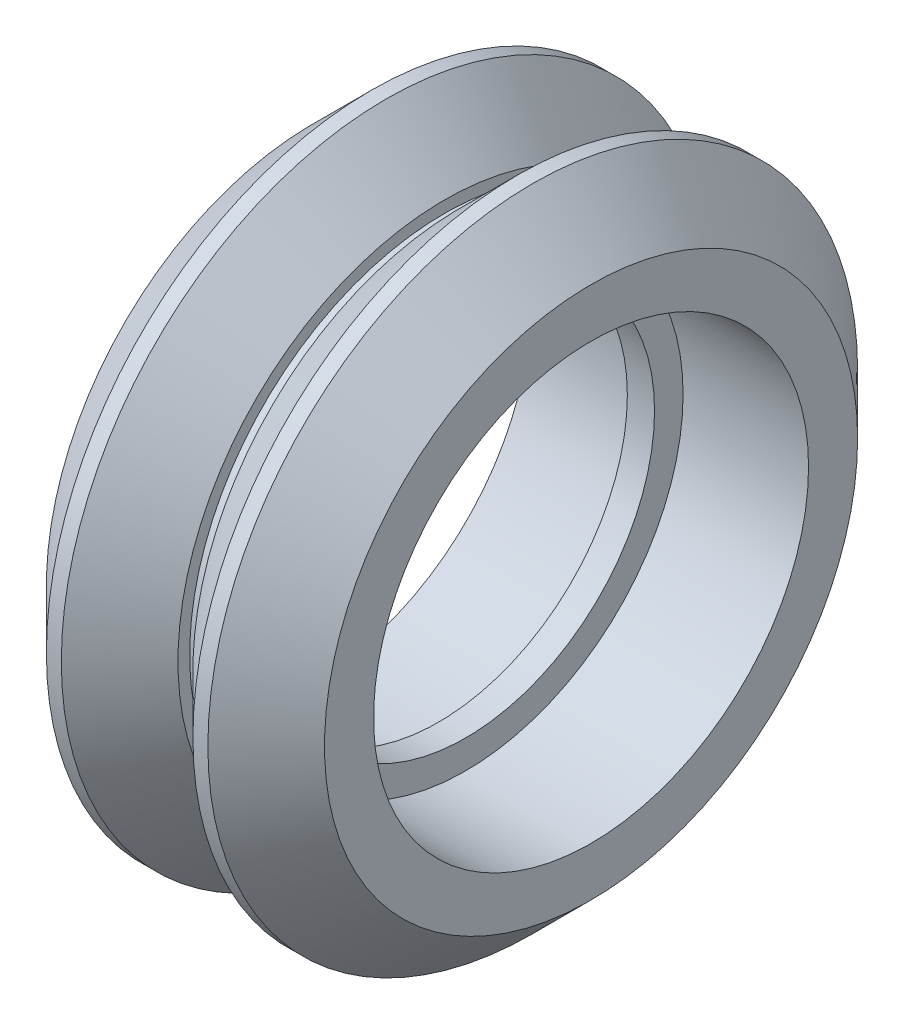
SolidWorks part; units mm, degrees
material "Chrome Stainless Steel"
ref_plane "Front Plane" through (0, 0, 0) normal (0, 0, 1) x (1, 0, 0)
ref_plane "Top Plane" through (0, 0, 0) normal (0, 1, 0) x (1, 0, 0)
ref_plane "Right Plane" through (0, 0, 0) normal (1, 0, 0) x (0, 0, -1)
sketch "Sketch1" plane through (0, 0, 0) normal (0, 0, 1) x (1, 0, 0)
  line L0 (0.5, 6.95) -> (-0.5, 6.95)
  line L1 (-0.5, 6.95) -> (-0.5, 8)
  line L2 (-0.5, 8) -> (-5.115, 8)
  line L3 (-5.115, 8) -> (-5.115, 9.805)
  line L4 (-5.115, 9.805) -> (-2.97, 11.95)
  line L5 (-2.97, 11.95) -> (-2.42, 11.95)
  line L6 (0, 12) -> (0, 6.95) construction
  line L7 (5.115, 9.805) -> (2.97, 11.95)
  line L8 (5.115, 8) -> (5.115, 9.805)
  line L9 (0.5, 8) -> (5.115, 8)
  line L10 (0.5, 6.95) -> (0.5, 8)
  line L11 (0, 0) -> (-12.6359, 0) construction
  line L12 (-2.42, 11.95) -> (-0.275, 9.805)
  line L13 (-0.275, 9.805) -> (-0.275, 9.375)
  line L14 (-0.275, 9.375) -> (0.275, 9.375)
  line L15 (0.275, 9.805) -> (0.275, 9.375)
  line L16 (2.97, 11.95) -> (2.42, 11.95)
  line L17 (2.42, 11.95) -> (0.275, 9.805)
  point P20 (0, 9.375)
  dimension "D1" = 0.55
  dimension "D2" = 16
  dimension "D3" = 23.9
  dimension "D4" = 1
  dimension "D5" = 45
  dimension "D6" = 10.23
  dimension "D7" = 18.75
  dimension "D8" = 13.9
revolve "Revolve1" add sketch "Sketch1" angle 360 about L11
